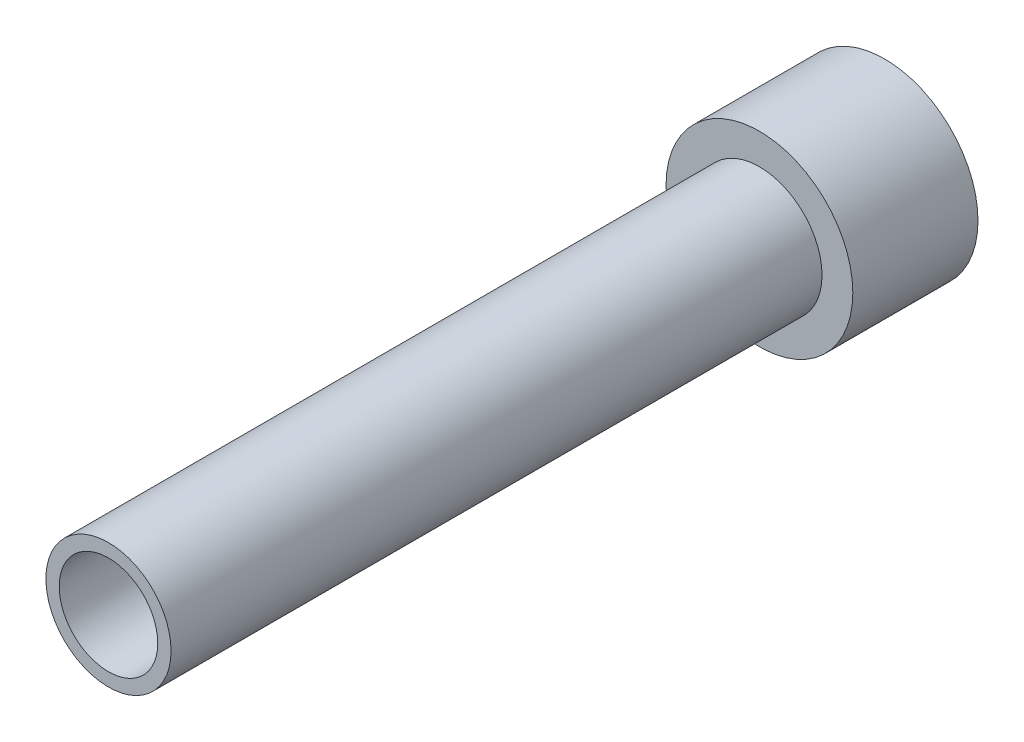
SolidWorks part; units mm, degrees
ref_plane "Front Plane" through (0, 0, 0) normal (0, 0, 1) x (1, 0, 0)
ref_plane "Top Plane" through (0, 0, 0) normal (0, 1, 0) x (1, 0, 0)
ref_plane "Right Plane" through (0, 0, 0) normal (1, 0, 0) x (0, 0, -1)
sketch "Sketch1" plane through (0, 0, 0) normal (0, 0, 1) x (1, 0, 0)
  circle A0 centre (0, 0) radius 2.5
  circle A1 centre (0, 0) radius 4.7371
  dimension "D1" = 5
  dimension "D2" = 9.4742
extrude "Boss-Extrude1" add sketch "Sketch1" along normal blind 6.35
sketch "Sketch2" plane through (0, 0, 6.35) normal (0, 0, 1) x (1, 0, 0)
  circle A0 centre (0, 0) radius 2.5
  circle A1 centre (0, 0) radius 3.175
  dimension "D1" = 6.35
extrude "Boss-Extrude2" add sketch "Sketch2" along normal blind 33.02
ref_plane "Plane1" through (-4.7371, 0, 0) normal (-1, 0, 0) x (0, 0, 1)
hole_wizard "#4-40 Tapped Hole1" positions "Sketch5" profile "Sketch4" tap size "#4-40" standard "Ansi Inch"
sketch "Sketch5" plane through (-4.7371, 0, 0) normal (-1, 0, 0) x (0, 0, 1)
  line L6 (3.1916, 7.2836) -> (3.1916, -10.958) construction
  line L9 (7.193, 0) -> (-1.2805, 0) construction
  point P1 (3.1916, 0)
sketch "Sketch4" plane through (-4.7371, 0, 3.1916) normal (0, 1, 0) x (0, 0, 1)
  line L0 (0, 0) -> (0, 5.4153)
  line L1 (0, 5.4153) -> (1.1303, 4.7361)
  line L2 (1.1303, 4.7361) -> (1.1303, 0)
  line L5 (1.1303, 0) -> (0, 0)
  line L10 (0, 5.4153) -> (-1.1303, 4.7361) construction
  line L11 (0, -6.35) -> (0, 107.95) construction
  dimension "Tap Drill Dia." = 2.2606
  dimension "Tap Drill Depth" = 4.7361
  dimension "Drill Angle" = 118
ref_plane "Plane2" through (-3.175, 0, 0) normal (-1, 0, 0) x (0, 0, 1)
sketch "Sketch6" plane through (0, 0, 6.35) normal (0, 0, 1) x (1, 0, 0)
  circle A0 centre (0, 0) radius 4.7371
  circle A1 centre (0, 0) radius 3.175
